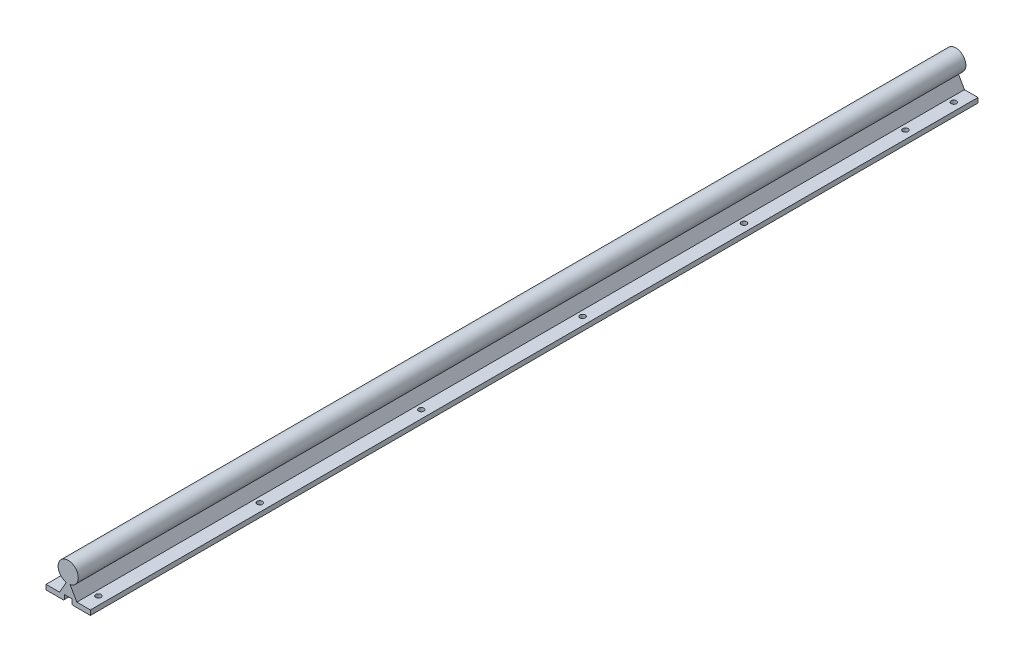
SolidWorks part; units mm, degrees
material "1060 Alloy"
ref_plane "Front Plane" through (0, 0, 0) normal (0, 0, 1) x (1, 0, 0)
ref_plane "Top Plane" through (0, 0, 0) normal (0, 1, 0) x (1, 0, 0)
ref_plane "Right Plane" through (0, 0, 0) normal (1, 0, 0) x (0, 0, -1)
sketch "Sketch1" plane through (0, 0, 0) normal (0, 0, 1) x (1, 0, 0)
  line L0 (-27.5, 0) -> (-4.75, 0)
  line L1 (10.75, 6) -> (2.0897, 21)
  line L2 (-4.75, 0) -> (-4.75, 6.5)
  line L3 (-4.75, 6.5) -> (4.75, 6.5)
  line L4 (-27.5, 0) -> (-27.5, 6)
  line L5 (-27.5, 6) -> (-10.75, 6)
  line L6 (-10.75, 6) -> (-2.0897, 21)
  line L7 (-2.0897, 21) -> (2.0897, 21)
  line L8 (0, 0) -> (0, 50.9475) construction
  line L9 (27.5, 6) -> (10.75, 6)
  line L10 (27.5, 0) -> (27.5, 6)
  line L11 (4.75, 0) -> (4.75, 6.5)
  line L12 (27.5, 0) -> (4.75, 0)
  circle A0 centre (0, 33) radius 12.5
  point P21 (0, 21)
  point P25 (0, 6.5)
  dimension "D1" = 55
  dimension "D5" = 25
  dimension "D2" = 21
  dimension "D3" = 6
  dimension "D4" = 6.5
  dimension "D6" = 21.5
  dimension "D7" = 9.5
  dimension "D8" = 30
  dimension "D9" = 33
extrude "Boss-Extrude1" add sketch "Sketch1" against normal blind 1100 contours L7 L8 A0 L6 | L8 L7 L1 A0 | L8 L3 L11 L12 L10 L9 L1 A0 | L3 L8 A0 L6 L5 L4 L0 L2 | L8 A0 L1 L7 | A0 L8 L7 L6
chamfer "Chamfer1" distance 1 angle 45 2 edges at (-4.75, 0, -550) (4.75, 0, -550)
sketch "Sketch2" plane through (0, 6, 0) normal (0, 1, 0) x (1, 0, 0)
  line L0 (27.5, 0) -> (10.75, 0) construction
  line L1 (0, 0) -> (0, 13.9025) construction
  line L2 (27.5, 1100) -> (10.75, 1100) construction
  line L3 (0, 1100) -> (0, 1839.438) construction
  line L4 (12.5, 1100) -> (-12.5, 1100) construction
  circle A0 centre (17.5, 20) radius 3.3
  circle A1 centre (-17.5, 20) radius 3.3
  circle A2 centre (-17.5, 220) radius 3.3
  circle A3 centre (17.5, 220) radius 3.3
  circle A4 centre (-17.5, 420) radius 3.3
  circle A5 centre (17.5, 420) radius 3.3
  circle A6 centre (-17.5, 620) radius 3.3
  circle A7 centre (17.5, 620) radius 3.3
  circle A8 centre (-17.5, 820) radius 3.3
  circle A9 centre (17.5, 820) radius 3.3
  circle A10 centre (-17.5, 1020) radius 3.3
  circle A11 centre (17.5, 1020) radius 3.3
  circle A12 centre (-17.5, 1220) radius 3.3
  circle A13 centre (17.5, 1220) radius 3.3
  circle A14 centre (-17.5, 1420) radius 3.3
  circle A15 centre (17.5, 1420) radius 3.3
  circle A16 centre (-17.5, 1620) radius 3.3
  circle A17 centre (17.5, 1620) radius 3.3
  circle A20 centre (17.5, 1080) radius 3.3
  circle A21 centre (-17.5, 1080) radius 3.3
  point P53 (0, 1100)
  dimension "D1" = 6.6
  dimension "D6" = 6.6
  dimension "D2" = 20
  dimension "D3" = 35
  dimension "D5" = 200
  dimension "D7" = 20
  dimension "D4" = 9
extrude "Cut-Extrude1" cut sketch "Sketch2" against normal through all both and the other way through all
